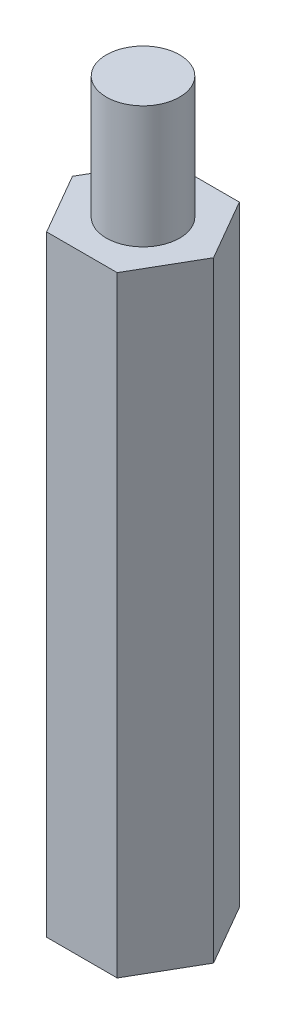
SolidWorks part; units mm, degrees
ref_plane "Front" through (0, 0, 0) normal (0, 0, 1) x (1, 0, 0)
ref_plane "Top" through (0, 0, 0) normal (0, 1, 0) x (1, 0, 0)
ref_plane "Right" through (0, 0, 0) normal (1, 0, 0) x (0, 0, -1)
sketch "草圖1" plane through (0, 0, 0) normal (0, 1, 0) x (1, 0, 0)
  line L1 (2.8868, 0) -> (1.4434, 2.5)
  line L2 (1.4434, 2.5) -> (-1.4434, 2.5)
  line L3 (-1.4434, 2.5) -> (-2.8868, 0)
  line L4 (-2.8868, 0) -> (-1.4434, -2.5)
  line L5 (-1.4434, -2.5) -> (1.4434, -2.5)
  line L6 (1.4434, -2.5) -> (2.8868, 0)
  circle A0 centre (0, 0) radius 2.5 construction
  dimension "D1" = 5
extrude "填料-伸長1" add sketch "草圖1" along normal blind 25
sketch "草圖2" plane through (0, 25, 0) normal (0, 1, 0) x (1, 0, 0)
  circle A0 centre (0, 0) radius 1.5
  dimension "D1" = 3
extrude "填料-伸長2" add sketch "草圖2" along normal blind 5
sketch "草圖3" plane through (0, 0, 0) normal (0, -1, 0) x (1, 0, 0)
  circle A0 centre (0, 0) radius 1.5
  dimension "D1" = 3
extrude "除料-伸長1" cut sketch "草圖3" against normal blind 5
